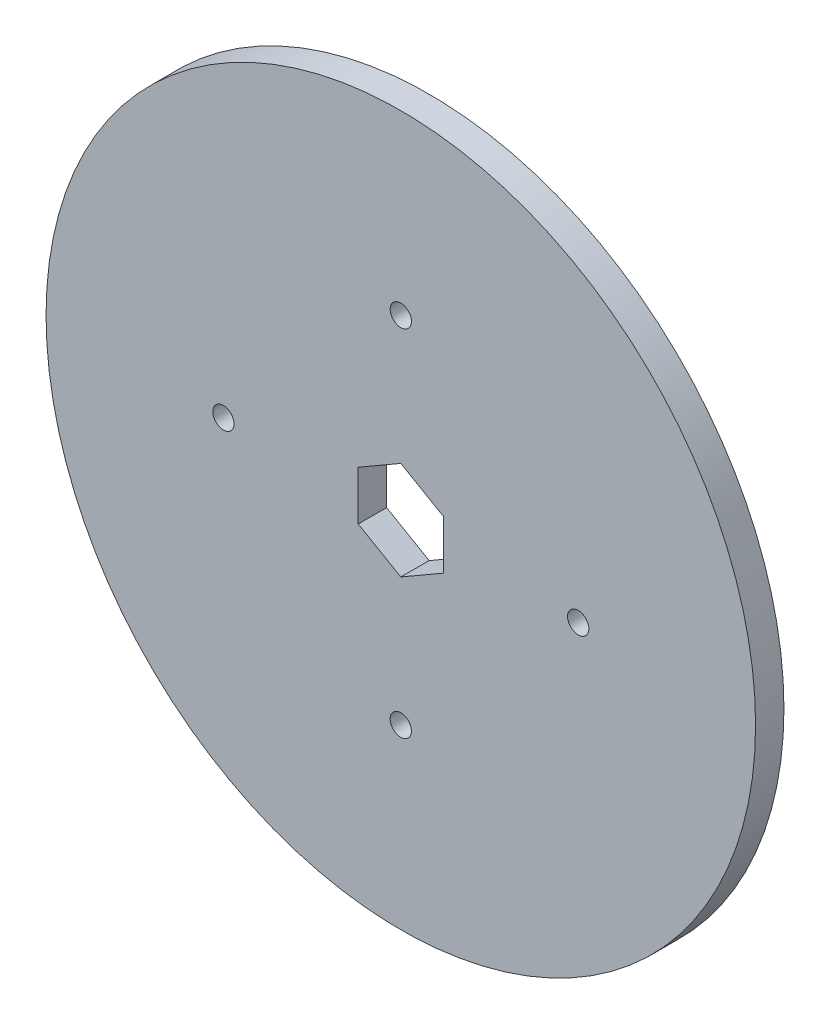
SolidWorks part; units mm, degrees
ref_plane "Front Plane" through (0, 0, 0) normal (0, 0, 1) x (1, 0, 0)
ref_plane "Top Plane" through (0, 0, 0) normal (0, 1, 0) x (1, 0, 0)
ref_plane "Right Plane" through (0, 0, 0) normal (1, 0, 0) x (0, 0, -1)
sketch "Sketch1" plane through (0, 0, 0) normal (0, 0, 1) x (1, 0, 0)
  circle A0 centre (-42.2867, 29.939) radius 50
  dimension "D1" = 100
extrude "Boss-Extrude1" add sketch "Sketch1" along normal blind 4 contours A0
sketch "Sketch4" plane through (0, 0, 4) normal (0, 0, 1) x (1, 0, 0)
  line L1 (-42.2867, 23.0108) -> (-36.2867, 26.4749)
  line L2 (-36.2867, 26.4749) -> (-36.2867, 33.4031)
  line L3 (-36.2867, 33.4031) -> (-42.2867, 36.8672)
  line L4 (-42.2867, 36.8672) -> (-48.2867, 33.4031)
  line L5 (-48.2867, 33.4031) -> (-48.2867, 26.4749)
  line L6 (-48.2867, 26.4749) -> (-42.2867, 23.0108)
  circle A0 centre (-42.2867, 29.939) radius 6 construction
  dimension "D2" = 12
extrude "Cut-Extrude1" cut sketch "Sketch4" against normal blind 12
sketch "Sketch5" plane through (0, 0, 4) normal (0, 0, 1) x (1, 0, 0)
  circle A1 centre (-67.2867, 29.939) radius 1.5
  circle A2 centre (-42.2867, 54.939) radius 1.5
  circle A3 centre (-17.2867, 29.939) radius 1.5
  circle A4 centre (-42.2867, 4.939) radius 1.5
  point P11 (-42.2867, 29.939)
  dimension "D1" = 4
extrude "Cut-Extrude2" cut sketch "Sketch5" against normal blind 4
